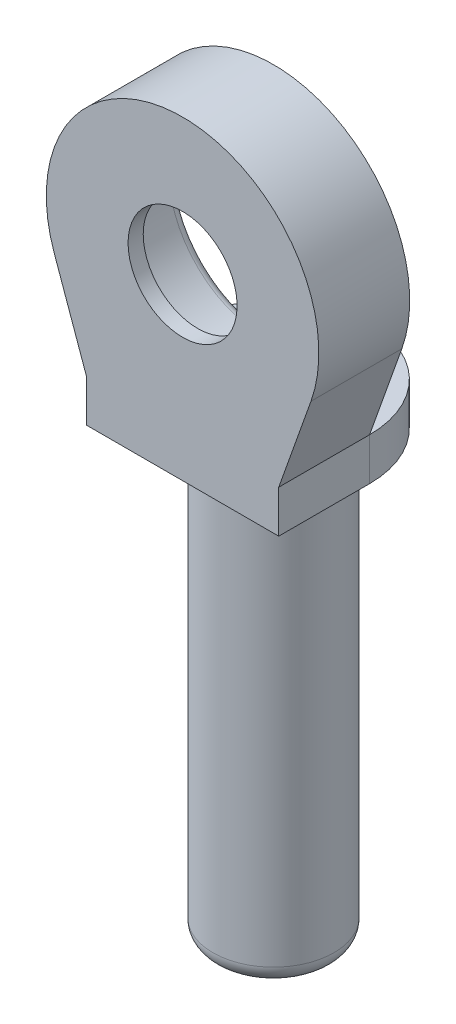
SolidWorks part; units mm, degrees
ref_plane "前视基准面" through (0, 0, 0) normal (0, 0, 1) x (1, 0, 0)
ref_plane "上视基准面" through (0, 0, 0) normal (0, 1, 0) x (1, 0, 0)
ref_plane "右视基准面" through (0, 0, 0) normal (1, 0, 0) x (0, 0, -1)
ref_plane "基准面1" through (0, 0, 0.5) normal (0, 0, 1) x (1, 0, 0)
sketch "草图1" plane through (0, 0, 0) normal (0, 1, 0) x (1, 0, 0)
  line L0 (0, 0) -> (0, 4.3268) construction
  line L1 (0, 0) -> (6.0935, 0) construction
  circle A0 centre (0, 0) radius 2
  dimension "D1" = 4
extrude "凸台-拉伸1" add sketch "草图1" along normal blind 16
sketch "草图2" plane through (0, 0, 0) normal (0, 0, 1) x (1, 0, 0)
  line L2 (-2.327, 16) -> (-3.6912, 16) construction
  line L3 (2, 16) -> (-2, 16) construction
  line L7 (0, 0) -> (0, 34.2634) construction
  arc A0 (4.2457, 21.9912) -> (0, 16) centre (0, 20.5) ccw
  arc A2 (4.2457, 21.9912) -> (0, 16) centre (0, 20.5) cw
  dimension "D1" = 4.5
  dimension "D2" = 9
extrude "凸台-拉伸2" add sketch "草图2" along normal blind 3
sketch "草图4" plane through (0, 0, 0) normal (0, 0, -1) x (-1, 0, 0)
  circle A0 centre (0, 20.5) radius 3.15
  dimension "D1" = 6.3
extrude "切除-拉伸6" cut sketch "草图4" against normal blind 2.5
fillet "圆角3" radius 0.6 1 edges at (0, 0, 2)
sketch "草图7" plane through (0, 16, 0) normal (0, 1, 0) x (1, 0, 0)
  circle A0 centre (0, 0) radius 3.175
  dimension "D1" = 6.35
extrude "凸台-拉伸3" add sketch "草图7" against normal blind 1.4
sketch "草图10" plane through (0, 0, 0) normal (0, -1, 0) x (1, 0, 0)
  line L0 (-3.1354, 0.5) -> (1.6694, 0.5) construction
  line L6 (-1.3077, 0.5) -> (1.3077, 0.5)
  arc A0 (-1.3077, 0.5) -> (1.3077, 0.5) centre (0, 0) ccw
  circle A2 centre (0, 0) radius 3.175 construction
  dimension "D1" = 1.4
  dimension "D2" = 0.5
extrude "切除-拉伸9" cut sketch "草图10" against normal through all both and the other way through all
fillet "圆角6" radius 1 1 edges at (0, 16, -1.4)
sketch "草图12" plane through (0, 0, 3) normal (0, 0, 1) x (1, 0, 0)
  line L0 (-3.175, 16) -> (-4.2395, 18.9912)
  line L2 (0, 20.5) -> (-4.2395, 18.9912) construction
  line L3 (0, 20.5) -> (4.2395, 18.9912) construction
  line L4 (-3.175, 16) -> (-3.175, 14.6)
  line L5 (-3.175, 14.6) -> (3.175, 14.6)
  line L6 (3.175, 14.6) -> (3.175, 16)
  line L7 (3.175, 16) -> (4.2395, 18.9912)
  circle A0 centre (0, 20.5) radius 4.5 construction
  arc A1 (-4.2395, 18.9912) -> (4.2395, 18.9912) centre (0, 20.5) ccw
extrude "凸台-拉伸5" add sketch "草图12" against normal up to surface (3 mm away) up to face at (-3.15, 20.5, 0)
fillet "圆角7" radius 0.3 1 edges at (-3.15, 20.5, 0)
sketch "草图13" plane through (0, 0, 2.5) normal (0, 0, -1) x (-1, 0, 0)
  circle A0 centre (0, 20.5) radius 1.8
  dimension "D1" = 3.6
extrude "切除-拉伸10" cut sketch "草图13" against normal up to next
sketch "草图14" plane through (0, 16, 0) normal (0, 1, 0) x (1, 0, 0)
  line L0 (-1.0395, -3) -> (1.0395, -3)
  line L1 (1.0395, -3) -> (1.0395, -3.4918)
  line L2 (1.0395, -3.4918) -> (-1.0395, -3.4918)
  line L3 (-1.0395, -3.4918) -> (-1.0395, -3)
extrude "切除-拉伸11" cut sketch "草图14" against normal up to next
